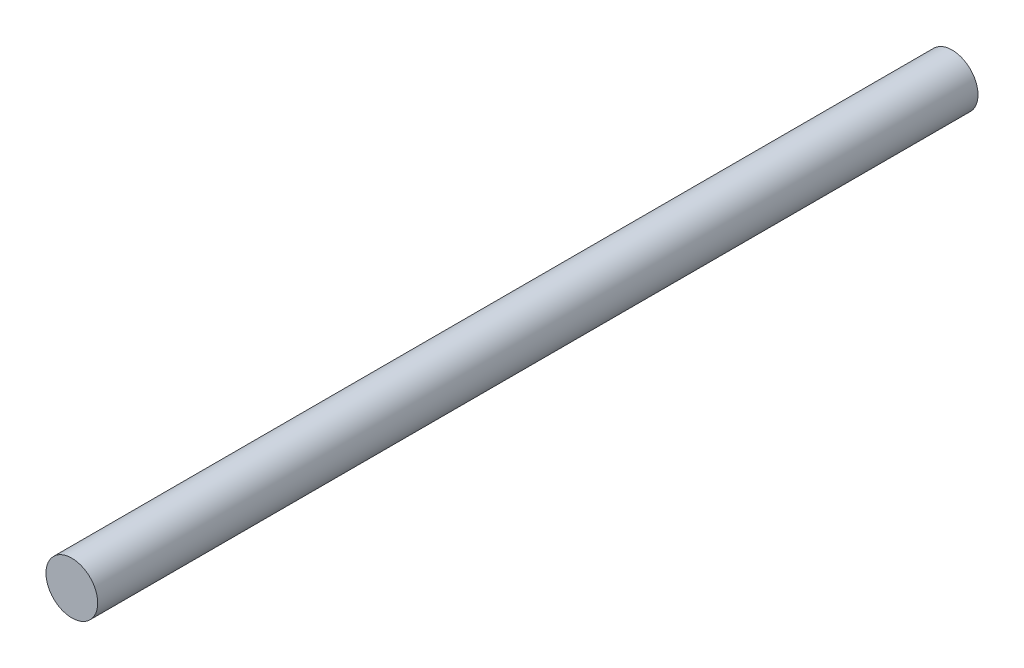
SolidWorks part; units mm, degrees
material "Plain Carbon Steel"
ref_plane "Front Plane" through (0, 0, 0) normal (0, 0, 1) x (1, 0, 0)
ref_plane "Top Plane" through (0, 0, 0) normal (0, 1, 0) x (1, 0, 0)
ref_plane "Right Plane" through (0, 0, 0) normal (1, 0, 0) x (0, 0, -1)
sketch "Sketch1" plane through (0, 0, 0) normal (0, 0, 1) x (1, 0, 0)
  circle A0 centre (0, 0) radius 4
extrude "Boss-Extrude1" add sketch "Sketch1" along normal blind 136
